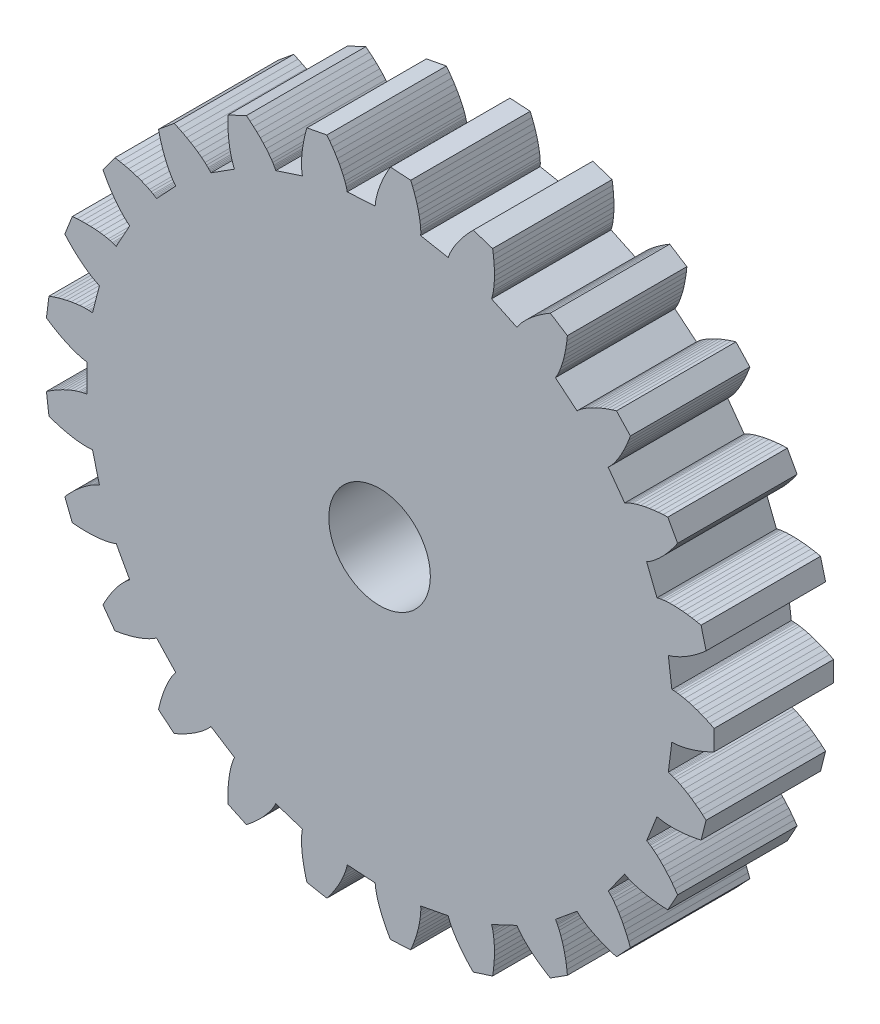
SolidWorks part; units mm, degrees
ref_plane "Front Plane" through (0, 0, 0) normal (0, 0, 1) x (1, 0, 0)
ref_plane "Top Plane" through (0, 0, 0) normal (0, 1, 0) x (1, 0, 0)
ref_plane "Right Plane" through (0, 0, 0) normal (1, 0, 0) x (0, 0, -1)
sketch "Model" plane through (0, 0, 0) normal (0, 0, 1) x (1, 0, 0)
  line L0 (22.5153, 13.4937) -> (22.5501, 13.4944)
  line L1 (22.5501, 13.4944) -> (22.5851, 13.4936)
  line L2 (22.5851, 13.4936) -> (22.6201, 13.4916)
  line L3 (22.6201, 13.4916) -> (22.6552, 13.4888)
  line L4 (22.6552, 13.4888) -> (22.7255, 13.481)
  line L5 (22.7255, 13.481) -> (22.796, 13.4706)
  line L6 (22.796, 13.4706) -> (22.9373, 13.4433)
  line L7 (22.9373, 13.4433) -> (23.079, 13.4085)
  line L8 (23.079, 13.4085) -> (23.221, 13.3669)
  line L9 (23.221, 13.3669) -> (23.363, 13.3191)
  line L10 (23.363, 13.3191) -> (23.5051, 13.2655)
  line L11 (23.5051, 13.2655) -> (23.647, 13.2062)
  line L12 (23.647, 13.2062) -> (23.7888, 13.1416)
  line L13 (23.7888, 13.1416) -> (23.9303, 13.0718)
  line L14 (23.9303, 13.0718) -> (23.9303, 12.3915)
  line L15 (23.9303, 12.3915) -> (23.7888, 12.3217)
  line L16 (23.7888, 12.3217) -> (23.647, 12.257)
  line L17 (23.647, 12.257) -> (23.5051, 12.1978)
  line L18 (23.5051, 12.1978) -> (23.363, 12.1441)
  line L19 (23.363, 12.1441) -> (23.221, 12.0963)
  line L20 (23.221, 12.0963) -> (23.079, 12.0548)
  line L21 (23.079, 12.0548) -> (22.9373, 12.0199)
  line L22 (22.9373, 12.0199) -> (22.796, 11.9927)
  line L23 (22.796, 11.9927) -> (22.7255, 11.9823)
  line L24 (22.7255, 11.9823) -> (22.6552, 11.9745)
  line L25 (22.6552, 11.9745) -> (22.6201, 11.9716)
  line L26 (22.6201, 11.9716) -> (22.5851, 11.9697)
  line L27 (22.5851, 11.9697) -> (22.5501, 11.9688)
  line L28 (22.5501, 11.9688) -> (22.5153, 11.9696)
  line L29 (22.5153, 11.9696) -> (22.3975, 11.0367)
  line L30 (22.3975, 11.0367) -> (22.4314, 11.0287)
  line L31 (22.4314, 11.0287) -> (22.465, 11.0192)
  line L32 (22.465, 11.0192) -> (22.4984, 11.0086)
  line L33 (22.4984, 11.0086) -> (22.5317, 10.9971)
  line L34 (22.5317, 10.9971) -> (22.5978, 10.9721)
  line L35 (22.5978, 10.9721) -> (22.6635, 10.9445)
  line L36 (22.6635, 10.9445) -> (22.7937, 10.8829)
  line L37 (22.7937, 10.8829) -> (22.9223, 10.8139)
  line L38 (22.9223, 10.8139) -> (23.0494, 10.7384)
  line L39 (23.0494, 10.7384) -> (23.1751, 10.6567)
  line L40 (23.1751, 10.6567) -> (23.2994, 10.5694)
  line L41 (23.2994, 10.5694) -> (23.4221, 10.4767)
  line L42 (23.4221, 10.4767) -> (23.5434, 10.3789)
  line L43 (23.5434, 10.3789) -> (23.6631, 10.2761)
  line L44 (23.6631, 10.2761) -> (23.4939, 9.6172)
  line L45 (23.4939, 9.6172) -> (23.3395, 9.5847)
  line L46 (23.3395, 9.5847) -> (23.1861, 9.5574)
  line L47 (23.1861, 9.5574) -> (23.0339, 9.5353)
  line L48 (23.0339, 9.5353) -> (22.8829, 9.5187)
  line L49 (22.8829, 9.5187) -> (22.7334, 9.5077)
  line L50 (22.7334, 9.5077) -> (22.5856, 9.5027)
  line L51 (22.5856, 9.5027) -> (22.4397, 9.5042)
  line L52 (22.4397, 9.5042) -> (22.296, 9.513)
  line L53 (22.296, 9.513) -> (22.2251, 9.5205)
  line L54 (22.2251, 9.5205) -> (22.1551, 9.5304)
  line L55 (22.1551, 9.5304) -> (22.1204, 9.5364)
  line L56 (22.1204, 9.5364) -> (22.086, 9.5432)
  line L57 (22.086, 9.5432) -> (22.0519, 9.551)
  line L58 (22.0519, 9.551) -> (22.0184, 9.5604)
  line L59 (22.0184, 9.5604) -> (21.6723, 8.6861)
  line L60 (21.6723, 8.6861) -> (21.7031, 8.67)
  line L61 (21.7031, 8.67) -> (21.7333, 8.6524)
  line L62 (21.7333, 8.6524) -> (21.7631, 8.6338)
  line L63 (21.7631, 8.6338) -> (21.7925, 8.6145)
  line L64 (21.7925, 8.6145) -> (21.8503, 8.5737)
  line L65 (21.8503, 8.5737) -> (21.9071, 8.5306)
  line L66 (21.9071, 8.5306) -> (22.0178, 8.4387)
  line L67 (22.0178, 8.4387) -> (22.1252, 8.3399)
  line L68 (22.1252, 8.3399) -> (22.2296, 8.2351)
  line L69 (22.2296, 8.2351) -> (22.331, 8.1247)
  line L70 (22.331, 8.1247) -> (22.4297, 8.0093)
  line L71 (22.4297, 8.0093) -> (22.5255, 7.889)
  line L72 (22.5255, 7.889) -> (22.6186, 7.764)
  line L73 (22.6186, 7.764) -> (22.709, 7.6347)
  line L74 (22.709, 7.6347) -> (22.3812, 7.0385)
  line L75 (22.3812, 7.0385) -> (22.2236, 7.0455)
  line L76 (22.2236, 7.0455) -> (22.0683, 7.0572)
  line L77 (22.0683, 7.0572) -> (21.9153, 7.0737)
  line L78 (21.9153, 7.0737) -> (21.765, 7.0951)
  line L79 (21.765, 7.0951) -> (21.6175, 7.1216)
  line L80 (21.6175, 7.1216) -> (21.473, 7.1536)
  line L81 (21.473, 7.1536) -> (21.3321, 7.1913)
  line L82 (21.3321, 7.1913) -> (21.1951, 7.2356)
  line L83 (21.1951, 7.2356) -> (21.1283, 7.2604)
  line L84 (21.1283, 7.2604) -> (21.0629, 7.2874)
  line L85 (21.0629, 7.2874) -> (21.0308, 7.3018)
  line L86 (21.0308, 7.3018) -> (20.9992, 7.317)
  line L87 (20.9992, 7.317) -> (20.9681, 7.3331)
  line L88 (20.9681, 7.3331) -> (20.938, 7.3505)
  line L89 (20.938, 7.3505) -> (20.3853, 6.5898)
  line L90 (20.3853, 6.5898) -> (20.4112, 6.5665)
  line L91 (20.4112, 6.5665) -> (20.4361, 6.5419)
  line L92 (20.4361, 6.5419) -> (20.4602, 6.5165)
  line L93 (20.4602, 6.5165) -> (20.4839, 6.4905)
  line L94 (20.4839, 6.4905) -> (20.5298, 6.4366)
  line L95 (20.5298, 6.4366) -> (20.574, 6.3808)
  line L96 (20.574, 6.3808) -> (20.6584, 6.2642)
  line L97 (20.6584, 6.2642) -> (20.7379, 6.1418)
  line L98 (20.7379, 6.1418) -> (20.8129, 6.0143)
  line L99 (20.8129, 6.0143) -> (20.8838, 5.8822)
  line L100 (20.8838, 5.8822) -> (20.9506, 5.7458)
  line L101 (20.9506, 5.7458) -> (21.0135, 5.6055)
  line L102 (21.0135, 5.6055) -> (21.0726, 5.4613)
  line L103 (21.0726, 5.4613) -> (21.128, 5.3136)
  line L104 (21.128, 5.3136) -> (20.6622, 4.8176)
  line L105 (20.6622, 4.8176) -> (20.5113, 4.8636)
  line L106 (20.5113, 4.8636) -> (20.3638, 4.9136)
  line L107 (20.3638, 4.9136) -> (20.2197, 4.9675)
  line L108 (20.2197, 4.9675) -> (20.0794, 5.0257)
  line L109 (20.0794, 5.0257) -> (19.9432, 5.0881)
  line L110 (19.9432, 5.0881) -> (19.8112, 5.1549)
  line L111 (19.8112, 5.1549) -> (19.6841, 5.2265)
  line L112 (19.6841, 5.2265) -> (19.5624, 5.3035)
  line L113 (19.5624, 5.3035) -> (19.5039, 5.3441)
  line L114 (19.5039, 5.3441) -> (19.4472, 5.3866)
  line L115 (19.4472, 5.3866) -> (19.4197, 5.4085)
  line L116 (19.4197, 5.4085) -> (19.3929, 5.4311)
  line L117 (19.3929, 5.4311) -> (19.3668, 5.4543)
  line L118 (19.3668, 5.4543) -> (19.3419, 5.4787)
  line L119 (19.3419, 5.4787) -> (18.6174, 4.8793)
  line L120 (18.6174, 4.8793) -> (18.6367, 4.8503)
  line L121 (18.6367, 4.8503) -> (18.6547, 4.8204)
  line L122 (18.6547, 4.8204) -> (18.6718, 4.7898)
  line L123 (18.6718, 4.7898) -> (18.6882, 4.7586)
  line L124 (18.6882, 4.7586) -> (18.7193, 4.6951)
  line L125 (18.7193, 4.6951) -> (18.7483, 4.63)
  line L126 (18.7483, 4.63) -> (18.801, 4.496)
  line L127 (18.801, 4.496) -> (18.8476, 4.3577)
  line L128 (18.8476, 4.3577) -> (18.8885, 4.2156)
  line L129 (18.8885, 4.2156) -> (18.9243, 4.07)
  line L130 (18.9243, 4.07) -> (18.9551, 3.9213)
  line L131 (18.9551, 3.9213) -> (18.9811, 3.7697)
  line L132 (18.9811, 3.7697) -> (19.0025, 3.6154)
  line L133 (19.0025, 3.6154) -> (19.0194, 3.4586)
  line L134 (19.0194, 3.4586) -> (18.445, 3.094)
  line L135 (18.445, 3.094) -> (18.3102, 3.1761)
  line L136 (18.3102, 3.1761) -> (18.1797, 3.2611)
  line L137 (18.1797, 3.2611) -> (18.0536, 3.3493)
  line L138 (18.0536, 3.3493) -> (17.9322, 3.4404)
  line L139 (17.9322, 3.4404) -> (17.8157, 3.5348)
  line L140 (17.8157, 3.5348) -> (17.7045, 3.6323)
  line L141 (17.7045, 3.6323) -> (17.5992, 3.7333)
  line L142 (17.5992, 3.7333) -> (17.5004, 3.8381)
  line L143 (17.5004, 3.8381) -> (17.4539, 3.892)
  line L144 (17.4539, 3.892) -> (17.4096, 3.9472)
  line L145 (17.4096, 3.9472) -> (17.3884, 3.9753)
  line L146 (17.3884, 3.9753) -> (17.368, 4.0038)
  line L147 (17.368, 4.0038) -> (17.3486, 4.0329)
  line L148 (17.3486, 4.0329) -> (17.3305, 4.0626)
  line L149 (17.3305, 4.0626) -> (16.4797, 3.6623)
  line L150 (16.4797, 3.6623) -> (16.4912, 3.6294)
  line L151 (16.4912, 3.6294) -> (16.5012, 3.5959)
  line L152 (16.5012, 3.5959) -> (16.5101, 3.562)
  line L153 (16.5101, 3.562) -> (16.5183, 3.5278)
  line L154 (16.5183, 3.5278) -> (16.5326, 3.4585)
  line L155 (16.5326, 3.4585) -> (16.5445, 3.3882)
  line L156 (16.5445, 3.3882) -> (16.5622, 3.2454)
  line L157 (16.5622, 3.2454) -> (16.5729, 3.0998)
  line L158 (16.5729, 3.0998) -> (16.5772, 2.952)
  line L159 (16.5772, 2.952) -> (16.5756, 2.8021)
  line L160 (16.5756, 2.8021) -> (16.5685, 2.6504)
  line L161 (16.5685, 2.6504) -> (16.556, 2.4971)
  line L162 (16.556, 2.4971) -> (16.5384, 2.3423)
  line L163 (16.5384, 2.3423) -> (16.5157, 2.1862)
  line L164 (16.5157, 2.1862) -> (15.8687, 1.9759)
  line L165 (15.8687, 1.9759) -> (15.7586, 2.0889)
  line L166 (15.7586, 2.0889) -> (15.6533, 2.2038)
  line L167 (15.6533, 2.2038) -> (15.5531, 2.3205)
  line L168 (15.5531, 2.3205) -> (15.4582, 2.439)
  line L169 (15.4582, 2.439) -> (15.3688, 2.5593)
  line L170 (15.3688, 2.5593) -> (15.2854, 2.6815)
  line L171 (15.2854, 2.6815) -> (15.2085, 2.8055)
  line L172 (15.2085, 2.8055) -> (15.1389, 2.9315)
  line L173 (15.1389, 2.9315) -> (15.1072, 2.9954)
  line L174 (15.1072, 2.9954) -> (15.078, 3.0598)
  line L175 (15.078, 3.0598) -> (15.0645, 3.0923)
  line L176 (15.0645, 3.0923) -> (15.0519, 3.125)
  line L177 (15.0519, 3.125) -> (15.0402, 3.158)
  line L178 (15.0402, 3.158) -> (15.0302, 3.1913)
  line L179 (15.0302, 3.1913) -> (14.1065, 3.0151)
  line L180 (14.1065, 3.0151) -> (14.1095, 2.9804)
  line L181 (14.1095, 2.9804) -> (14.1108, 2.9455)
  line L182 (14.1108, 2.9455) -> (14.111, 2.9104)
  line L183 (14.111, 2.9104) -> (14.1104, 2.8752)
  line L184 (14.1104, 2.8752) -> (14.107, 2.8046)
  line L185 (14.107, 2.8046) -> (14.1011, 2.7336)
  line L186 (14.1011, 2.7336) -> (14.0827, 2.5908)
  line L187 (14.0827, 2.5908) -> (14.0569, 2.4471)
  line L188 (14.0569, 2.4471) -> (14.0243, 2.3029)
  line L189 (14.0243, 2.3029) -> (13.9855, 2.1581)
  line L190 (13.9855, 2.1581) -> (13.9409, 2.0129)
  line L191 (13.9409, 2.0129) -> (13.8907, 1.8675)
  line L192 (13.8907, 1.8675) -> (13.8351, 1.722)
  line L193 (13.8351, 1.722) -> (13.7743, 1.5764)
  line L194 (13.7743, 1.5764) -> (13.0953, 1.5337)
  line L195 (13.0953, 1.5337) -> (13.0168, 1.6705)
  line L196 (13.0168, 1.6705) -> (12.9434, 1.808)
  line L197 (12.9434, 1.808) -> (12.8753, 1.9459)
  line L198 (12.8753, 1.9459) -> (12.8128, 2.0843)
  line L199 (12.8128, 2.0843) -> (12.7562, 2.2231)
  line L200 (12.7562, 2.2231) -> (12.7058, 2.3621)
  line L201 (12.7058, 2.3621) -> (12.6622, 2.5014)
  line L202 (12.6622, 2.5014) -> (12.6261, 2.6408)
  line L203 (12.6261, 2.6408) -> (12.6113, 2.7105)
  line L204 (12.6113, 2.7105) -> (12.599, 2.7801)
  line L205 (12.599, 2.7801) -> (12.594, 2.815)
  line L206 (12.594, 2.815) -> (12.5899, 2.8498)
  line L207 (12.5899, 2.8498) -> (12.5868, 2.8846)
  line L208 (12.5868, 2.8846) -> (12.5854, 2.9194)
  line L209 (12.5854, 2.9194) -> (11.6469, 2.9784)
  line L210 (11.6469, 2.9784) -> (11.6411, 2.9441)
  line L211 (11.6411, 2.9441) -> (11.6337, 2.91)
  line L212 (11.6337, 2.91) -> (11.6253, 2.8759)
  line L213 (11.6253, 2.8759) -> (11.6159, 2.842)
  line L214 (11.6159, 2.842) -> (11.595, 2.7744)
  line L215 (11.595, 2.7744) -> (11.5716, 2.7071)
  line L216 (11.5716, 2.7071) -> (11.5184, 2.5733)
  line L217 (11.5184, 2.5733) -> (11.4576, 2.4407)
  line L218 (11.4576, 2.4407) -> (11.3902, 2.309)
  line L219 (11.3902, 2.309) -> (11.3166, 2.1784)
  line L220 (11.3166, 2.1784) -> (11.2372, 2.049)
  line L221 (11.2372, 2.049) -> (11.1525, 1.9206)
  line L222 (11.1525, 1.9206) -> (11.0624, 1.7935)
  line L223 (11.0624, 1.7935) -> (10.9673, 1.6676)
  line L224 (10.9673, 1.6676) -> (10.2991, 1.7951)
  line L225 (10.2991, 1.7951) -> (10.257, 1.9471)
  line L226 (10.257, 1.9471) -> (10.2201, 2.0985)
  line L227 (10.2201, 2.0985) -> (10.1885, 2.249)
  line L228 (10.1885, 2.249) -> (10.1624, 2.3986)
  line L229 (10.1624, 2.3986) -> (10.1421, 2.5471)
  line L230 (10.1421, 2.5471) -> (10.1278, 2.6943)
  line L231 (10.1278, 2.6943) -> (10.1202, 2.8401)
  line L232 (10.1202, 2.8401) -> (10.1199, 2.984)
  line L233 (10.1199, 2.984) -> (10.1229, 3.0552)
  line L234 (10.1229, 3.0552) -> (10.1284, 3.1258)
  line L235 (10.1284, 3.1258) -> (10.1322, 3.1607)
  line L236 (10.1322, 3.1607) -> (10.1368, 3.1955)
  line L237 (10.1368, 3.1955) -> (10.1425, 3.23)
  line L238 (10.1425, 3.23) -> (10.1498, 3.264)
  line L239 (10.1498, 3.264) -> (9.2555, 3.5546)
  line L240 (9.2555, 3.5546) -> (9.2413, 3.5228)
  line L241 (9.2413, 3.5228) -> (9.2257, 3.4916)
  line L242 (9.2257, 3.4916) -> (9.209, 3.4607)
  line L243 (9.209, 3.4607) -> (9.1915, 3.4302)
  line L244 (9.1915, 3.4302) -> (9.1545, 3.3699)
  line L245 (9.1545, 3.3699) -> (9.1151, 3.3105)
  line L246 (9.1151, 3.3105) -> (9.0302, 3.1942)
  line L247 (9.0302, 3.1942) -> (8.9384, 3.0808)
  line L248 (8.9384, 3.0808) -> (8.8403, 2.9701)
  line L249 (8.8403, 2.9701) -> (8.7366, 2.8619)
  line L250 (8.7366, 2.8619) -> (8.6275, 2.7562)
  line L251 (8.6275, 2.7562) -> (8.5135, 2.653)
  line L252 (8.5135, 2.653) -> (8.3947, 2.5522)
  line L253 (8.3947, 2.5522) -> (8.2713, 2.4539)
  line L254 (8.2713, 2.4539) -> (7.6557, 2.7436)
  line L255 (7.6557, 2.7436) -> (7.6528, 2.9013)
  line L256 (7.6528, 2.9013) -> (7.6547, 3.0571)
  line L257 (7.6547, 3.0571) -> (7.6615, 3.2108)
  line L258 (7.6615, 3.2108) -> (7.6734, 3.3622)
  line L259 (7.6734, 3.3622) -> (7.6906, 3.5111)
  line L260 (7.6906, 3.5111) -> (7.7135, 3.6572)
  line L261 (7.7135, 3.6572) -> (7.7423, 3.8003)
  line L262 (7.7423, 3.8003) -> (7.7778, 3.9398)
  line L263 (7.7778, 3.9398) -> (7.7984, 4.008)
  line L264 (7.7984, 4.008) -> (7.8213, 4.0749)
  line L265 (7.8213, 4.0749) -> (7.8337, 4.1079)
  line L266 (7.8337, 4.1079) -> (7.8468, 4.1404)
  line L267 (7.8468, 4.1404) -> (7.8609, 4.1724)
  line L268 (7.8609, 4.1724) -> (7.8764, 4.2036)
  line L269 (7.8764, 4.2036) -> (7.0825, 4.7074)
  line L270 (7.0825, 4.7074) -> (7.0608, 4.6801)
  line L271 (7.0608, 4.6801) -> (7.0379, 4.6537)
  line L272 (7.0379, 4.6537) -> (7.0141, 4.628)
  line L273 (7.0141, 4.628) -> (6.9896, 4.6028)
  line L274 (6.9896, 4.6028) -> (6.9387, 4.5536)
  line L275 (6.9387, 4.5536) -> (6.8858, 4.5059)
  line L276 (6.8858, 4.5059) -> (6.7746, 4.4144)
  line L277 (6.7746, 4.4144) -> (6.6575, 4.3274)
  line L278 (6.6575, 4.3274) -> (6.535, 4.2445)
  line L279 (6.535, 4.2445) -> (6.4076, 4.1655)
  line L280 (6.4076, 4.1655) -> (6.2757, 4.0903)
  line L281 (6.2757, 4.0903) -> (6.1395, 4.0186)
  line L282 (6.1395, 4.0186) -> (5.9994, 3.9506)
  line L283 (5.9994, 3.9506) -> (5.8554, 3.8861)
  line L284 (5.8554, 3.8861) -> (5.3312, 4.3197)
  line L285 (5.3312, 4.3197) -> (5.3676, 4.4732)
  line L286 (5.3676, 4.4732) -> (5.4082, 4.6237)
  line L287 (5.4082, 4.6237) -> (5.453, 4.7708)
  line L288 (5.453, 4.7708) -> (5.5022, 4.9145)
  line L289 (5.5022, 4.9145) -> (5.556, 5.0544)
  line L290 (5.556, 5.0544) -> (5.6144, 5.1903)
  line L291 (5.6144, 5.1903) -> (5.6779, 5.3217)
  line L292 (5.6779, 5.3217) -> (5.747, 5.4479)
  line L293 (5.747, 5.4479) -> (5.7839, 5.5089)
  line L294 (5.7839, 5.5089) -> (5.8227, 5.5681)
  line L295 (5.8227, 5.5681) -> (5.8429, 5.5969)
  line L296 (5.8429, 5.5969) -> (5.8637, 5.6251)
  line L297 (5.8637, 5.6251) -> (5.8853, 5.6526)
  line L298 (5.8853, 5.6526) -> (5.9081, 5.6789)
  line L299 (5.9081, 5.6789) -> (5.2644, 6.3644)
  line L300 (5.2644, 6.3644) -> (5.2367, 6.3433)
  line L301 (5.2367, 6.3433) -> (5.2079, 6.3235)
  line L302 (5.2079, 6.3235) -> (5.1784, 6.3045)
  line L303 (5.1784, 6.3045) -> (5.1484, 6.2862)
  line L304 (5.1484, 6.2862) -> (5.0869, 6.2512)
  line L305 (5.0869, 6.2512) -> (5.0238, 6.2181)
  line L306 (5.0238, 6.2181) -> (4.8934, 6.1571)
  line L307 (4.8934, 6.1571) -> (4.7583, 6.102)
  line L308 (4.7583, 6.102) -> (4.619, 6.0522)
  line L309 (4.619, 6.0522) -> (4.476, 6.0074)
  line L310 (4.476, 6.0074) -> (4.3295, 5.9673)
  line L311 (4.3295, 5.9673) -> (4.1798, 5.9318)
  line L312 (4.1798, 5.9318) -> (4.0272, 5.9007)
  line L313 (4.0272, 5.9007) -> (3.8717, 5.874)
  line L314 (3.8717, 5.874) -> (3.4718, 6.4244)
  line L315 (3.4718, 6.4244) -> (3.5452, 6.5641)
  line L316 (3.5452, 6.5641) -> (3.6219, 6.6996)
  line L317 (3.6219, 6.6996) -> (3.7019, 6.831)
  line L318 (3.7019, 6.831) -> (3.7853, 6.9579)
  line L319 (3.7853, 6.9579) -> (3.8721, 7.0801)
  line L320 (3.8721, 7.0801) -> (3.9625, 7.1972)
  line L321 (3.9625, 7.1972) -> (4.0567, 7.3086)
  line L322 (4.0567, 7.3086) -> (4.1551, 7.4138)
  line L323 (4.1551, 7.4138) -> (4.206, 7.4636)
  line L324 (4.206, 7.4636) -> (4.2583, 7.5113)
  line L325 (4.2583, 7.5113) -> (4.285, 7.5342)
  line L326 (4.285, 7.5342) -> (4.3122, 7.5563)
  line L327 (4.3122, 7.5563) -> (4.3399, 7.5776)
  line L328 (4.3399, 7.5776) -> (4.3685, 7.5975)
  line L329 (4.3685, 7.5975) -> (3.9155, 8.4215)
  line L330 (3.9155, 8.4215) -> (3.8834, 8.4079)
  line L331 (3.8834, 8.4079) -> (3.8506, 8.3959)
  line L332 (3.8506, 8.3959) -> (3.8174, 8.3848)
  line L333 (3.8174, 8.3848) -> (3.7837, 8.3745)
  line L334 (3.7837, 8.3745) -> (3.7154, 8.3559)
  line L335 (3.7154, 8.3559) -> (3.6461, 8.3396)
  line L336 (3.6461, 8.3396) -> (3.5046, 8.3129)
  line L337 (3.5046, 8.3129) -> (3.36, 8.2932)
  line L338 (3.36, 8.2932) -> (3.2127, 8.2796)
  line L339 (3.2127, 8.2796) -> (3.0631, 8.2717)
  line L340 (3.0631, 8.2717) -> (2.9112, 8.2693)
  line L341 (2.9112, 8.2693) -> (2.7574, 8.2721)
  line L342 (2.7574, 8.2721) -> (2.6018, 8.28)
  line L343 (2.6018, 8.28) -> (2.4446, 8.2928)
  line L344 (2.4446, 8.2928) -> (2.1941, 8.9254)
  line L345 (2.1941, 8.9254) -> (2.3, 9.0424)
  line L346 (2.3, 9.0424) -> (2.408, 9.1547)
  line L347 (2.408, 9.1547) -> (2.5182, 9.262)
  line L348 (2.5182, 9.262) -> (2.6305, 9.3642)
  line L349 (2.6305, 9.3642) -> (2.745, 9.4609)
  line L350 (2.745, 9.4609) -> (2.8617, 9.5518)
  line L351 (2.8617, 9.5518) -> (2.9806, 9.6364)
  line L352 (2.9806, 9.6364) -> (3.102, 9.7138)
  line L353 (3.102, 9.7138) -> (3.1637, 9.7494)
  line L354 (3.1637, 9.7494) -> (3.2262, 9.7825)
  line L355 (3.2262, 9.7825) -> (3.2578, 9.7981)
  line L356 (3.2578, 9.7981) -> (3.2897, 9.8128)
  line L357 (3.2897, 9.8128) -> (3.3218, 9.8265)
  line L358 (3.3218, 9.8265) -> (3.3544, 9.8386)
  line L359 (3.3544, 9.8386) -> (3.1206, 10.7493)
  line L360 (3.1206, 10.7493) -> (3.0862, 10.7442)
  line L361 (3.0862, 10.7442) -> (3.0514, 10.7407)
  line L362 (3.0514, 10.7407) -> (3.0164, 10.7383)
  line L363 (3.0164, 10.7383) -> (2.9813, 10.7367)
  line L364 (2.9813, 10.7367) -> (2.9105, 10.7356)
  line L365 (2.9105, 10.7356) -> (2.8393, 10.7371)
  line L366 (2.8393, 10.7371) -> (2.6956, 10.7464)
  line L367 (2.6956, 10.7464) -> (2.5506, 10.7632)
  line L368 (2.5506, 10.7632) -> (2.4046, 10.7867)
  line L369 (2.4046, 10.7867) -> (2.2577, 10.8163)
  line L370 (2.2577, 10.8163) -> (2.11, 10.8517)
  line L371 (2.11, 10.8517) -> (1.9618, 10.8927)
  line L372 (1.9618, 10.8927) -> (1.813, 10.9391)
  line L373 (1.813, 10.9391) -> (1.6639, 10.9906)
  line L374 (1.6639, 10.9906) -> (1.5786, 11.6655)
  line L375 (1.5786, 11.6655) -> (1.7103, 11.7525)
  line L376 (1.7103, 11.7525) -> (1.8428, 11.8344)
  line L377 (1.8428, 11.8344) -> (1.9762, 11.911)
  line L378 (1.9762, 11.911) -> (2.1104, 11.982)
  line L379 (2.1104, 11.982) -> (2.2454, 12.0472)
  line L380 (2.2454, 12.0472) -> (2.381, 12.1063)
  line L381 (2.381, 12.1063) -> (2.5172, 12.1586)
  line L382 (2.5172, 12.1586) -> (2.654, 12.2034)
  line L383 (2.654, 12.2034) -> (2.7227, 12.2225)
  line L384 (2.7227, 12.2225) -> (2.7915, 12.2391)
  line L385 (2.7915, 12.2391) -> (2.8259, 12.2463)
  line L386 (2.8259, 12.2463) -> (2.8604, 12.2526)
  line L387 (2.8604, 12.2526) -> (2.8949, 12.2578)
  line L388 (2.8949, 12.2578) -> (2.9296, 12.2615)
  line L389 (2.9296, 12.2615) -> (2.9296, 13.2018)
  line L390 (2.9296, 13.2018) -> (2.8949, 13.2054)
  line L391 (2.8949, 13.2054) -> (2.8604, 13.2107)
  line L392 (2.8604, 13.2107) -> (2.8259, 13.217)
  line L393 (2.8259, 13.217) -> (2.7915, 13.2242)
  line L394 (2.7915, 13.2242) -> (2.7227, 13.2408)
  line L395 (2.7227, 13.2408) -> (2.654, 13.2599)
  line L396 (2.654, 13.2599) -> (2.5172, 13.3047)
  line L397 (2.5172, 13.3047) -> (2.381, 13.357)
  line L398 (2.381, 13.357) -> (2.2454, 13.416)
  line L399 (2.2454, 13.416) -> (2.1104, 13.4812)
  line L400 (2.1104, 13.4812) -> (1.9762, 13.5523)
  line L401 (1.9762, 13.5523) -> (1.8428, 13.6289)
  line L402 (1.8428, 13.6289) -> (1.7103, 13.7107)
  line L403 (1.7103, 13.7107) -> (1.5786, 13.7977)
  line L404 (1.5786, 13.7977) -> (1.6639, 14.4727)
  line L405 (1.6639, 14.4727) -> (1.813, 14.5242)
  line L406 (1.813, 14.5242) -> (1.9618, 14.5705)
  line L407 (1.9618, 14.5705) -> (2.11, 14.6115)
  line L408 (2.11, 14.6115) -> (2.2577, 14.647)
  line L409 (2.2577, 14.647) -> (2.4046, 14.6766)
  line L410 (2.4046, 14.6766) -> (2.5506, 14.7)
  line L411 (2.5506, 14.7) -> (2.6956, 14.7168)
  line L412 (2.6956, 14.7168) -> (2.8393, 14.7261)
  line L413 (2.8393, 14.7261) -> (2.9105, 14.7276)
  line L414 (2.9105, 14.7276) -> (2.9813, 14.7266)
  line L415 (2.9813, 14.7266) -> (3.0164, 14.725)
  line L416 (3.0164, 14.725) -> (3.0514, 14.7225)
  line L417 (3.0514, 14.7225) -> (3.0862, 14.719)
  line L418 (3.0862, 14.719) -> (3.1206, 14.7139)
  line L419 (3.1206, 14.7139) -> (3.3544, 15.6247)
  line L420 (3.3544, 15.6247) -> (3.3218, 15.6368)
  line L421 (3.3218, 15.6368) -> (3.2897, 15.6505)
  line L422 (3.2897, 15.6505) -> (3.2578, 15.6652)
  line L423 (3.2578, 15.6652) -> (3.2262, 15.6807)
  line L424 (3.2262, 15.6807) -> (3.1637, 15.7139)
  line L425 (3.1637, 15.7139) -> (3.102, 15.7495)
  line L426 (3.102, 15.7495) -> (2.9806, 15.8269)
  line L427 (2.9806, 15.8269) -> (2.8617, 15.9114)
  line L428 (2.8617, 15.9114) -> (2.745, 16.0023)
  line L429 (2.745, 16.0023) -> (2.6305, 16.0991)
  line L430 (2.6305, 16.0991) -> (2.5182, 16.2013)
  line L431 (2.5182, 16.2013) -> (2.408, 16.3086)
  line L432 (2.408, 16.3086) -> (2.3, 16.4209)
  line L433 (2.3, 16.4209) -> (2.1941, 16.5379)
  line L434 (2.1941, 16.5379) -> (2.4446, 17.1704)
  line L435 (2.4446, 17.1704) -> (2.6018, 17.1832)
  line L436 (2.6018, 17.1832) -> (2.7574, 17.1911)
  line L437 (2.7574, 17.1911) -> (2.9112, 17.1939)
  line L438 (2.9112, 17.1939) -> (3.0631, 17.1915)
  line L439 (3.0631, 17.1915) -> (3.2127, 17.1837)
  line L440 (3.2127, 17.1837) -> (3.36, 17.1701)
  line L441 (3.36, 17.1701) -> (3.5046, 17.1503)
  line L442 (3.5046, 17.1503) -> (3.6461, 17.1236)
  line L443 (3.6461, 17.1236) -> (3.7154, 17.1073)
  line L444 (3.7154, 17.1073) -> (3.7837, 17.0887)
  line L445 (3.7837, 17.0887) -> (3.8174, 17.0784)
  line L446 (3.8174, 17.0784) -> (3.8506, 17.0674)
  line L447 (3.8506, 17.0674) -> (3.8834, 17.0553)
  line L448 (3.8834, 17.0553) -> (3.9155, 17.0418)
  line L449 (3.9155, 17.0418) -> (4.3685, 17.8658)
  line L450 (4.3685, 17.8658) -> (4.3399, 17.8857)
  line L451 (4.3399, 17.8857) -> (4.3122, 17.9069)
  line L452 (4.3122, 17.9069) -> (4.285, 17.9291)
  line L453 (4.285, 17.9291) -> (4.2583, 17.952)
  line L454 (4.2583, 17.952) -> (4.206, 17.9996)
  line L455 (4.206, 17.9996) -> (4.1551, 18.0495)
  line L456 (4.1551, 18.0495) -> (4.0567, 18.1546)
  line L457 (4.0567, 18.1546) -> (3.9625, 18.2661)
  line L458 (3.9625, 18.2661) -> (3.8721, 18.3831)
  line L459 (3.8721, 18.3831) -> (3.7853, 18.5053)
  line L460 (3.7853, 18.5053) -> (3.7019, 18.6322)
  line L461 (3.7019, 18.6322) -> (3.6219, 18.7636)
  line L462 (3.6219, 18.7636) -> (3.5452, 18.8992)
  line L463 (3.5452, 18.8992) -> (3.4718, 19.0388)
  line L464 (3.4718, 19.0388) -> (3.8717, 19.5892)
  line L465 (3.8717, 19.5892) -> (4.0272, 19.5626)
  line L466 (4.0272, 19.5626) -> (4.1798, 19.5315)
  line L467 (4.1798, 19.5315) -> (4.3295, 19.496)
  line L468 (4.3295, 19.496) -> (4.476, 19.4559)
  line L469 (4.476, 19.4559) -> (4.619, 19.4111)
  line L470 (4.619, 19.4111) -> (4.7583, 19.3613)
  line L471 (4.7583, 19.3613) -> (4.8934, 19.3062)
  line L472 (4.8934, 19.3062) -> (5.0238, 19.2451)
  line L473 (5.0238, 19.2451) -> (5.0869, 19.2121)
  line L474 (5.0869, 19.2121) -> (5.1484, 19.1771)
  line L475 (5.1484, 19.1771) -> (5.1784, 19.1588)
  line L476 (5.1784, 19.1588) -> (5.2079, 19.1398)
  line L477 (5.2079, 19.1398) -> (5.2367, 19.1199)
  line L478 (5.2367, 19.1199) -> (5.2644, 19.0989)
  line L479 (5.2644, 19.0989) -> (5.9081, 19.7843)
  line L480 (5.9081, 19.7843) -> (5.8853, 19.8107)
  line L481 (5.8853, 19.8107) -> (5.8637, 19.8381)
  line L482 (5.8637, 19.8381) -> (5.8429, 19.8664)
  line L483 (5.8429, 19.8664) -> (5.8227, 19.8952)
  line L484 (5.8227, 19.8952) -> (5.7839, 19.9544)
  line L485 (5.7839, 19.9544) -> (5.747, 20.0153)
  line L486 (5.747, 20.0153) -> (5.6779, 20.1416)
  line L487 (5.6779, 20.1416) -> (5.6144, 20.273)
  line L488 (5.6144, 20.273) -> (5.556, 20.4089)
  line L489 (5.556, 20.4089) -> (5.5022, 20.5488)
  line L490 (5.5022, 20.5488) -> (5.453, 20.6925)
  line L491 (5.453, 20.6925) -> (5.4082, 20.8396)
  line L492 (5.4082, 20.8396) -> (5.3676, 20.99)
  line L493 (5.3676, 20.99) -> (5.3312, 21.1435)
  line L494 (5.3312, 21.1435) -> (5.8554, 21.5772)
  line L495 (5.8554, 21.5772) -> (5.9994, 21.5127)
  line L496 (5.9994, 21.5127) -> (6.1395, 21.4446)
  line L497 (6.1395, 21.4446) -> (6.2757, 21.373)
  line L498 (6.2757, 21.373) -> (6.4076, 21.2977)
  line L499 (6.4076, 21.2977) -> (6.535, 21.2188)
  line L500 (6.535, 21.2188) -> (6.6575, 21.1359)
  line L501 (6.6575, 21.1359) -> (6.7746, 21.0489)
  line L502 (6.7746, 21.0489) -> (6.8858, 20.9574)
  line L503 (6.8858, 20.9574) -> (6.9387, 20.9097)
  line L504 (6.9387, 20.9097) -> (6.9896, 20.8605)
  line L505 (6.9896, 20.8605) -> (7.0141, 20.8352)
  line L506 (7.0141, 20.8352) -> (7.0379, 20.8095)
  line L507 (7.0379, 20.8095) -> (7.0608, 20.7831)
  line L508 (7.0608, 20.7831) -> (7.0825, 20.7559)
  line L509 (7.0825, 20.7559) -> (7.8764, 21.2597)
  line L510 (7.8764, 21.2597) -> (7.8609, 21.2909)
  line L511 (7.8609, 21.2909) -> (7.8468, 21.3229)
  line L512 (7.8468, 21.3229) -> (7.8337, 21.3554)
  line L513 (7.8337, 21.3554) -> (7.8213, 21.3883)
  line L514 (7.8213, 21.3883) -> (7.7984, 21.4553)
  line L515 (7.7984, 21.4553) -> (7.7778, 21.5235)
  line L516 (7.7778, 21.5235) -> (7.7423, 21.663)
  line L517 (7.7423, 21.663) -> (7.7135, 21.806)
  line L518 (7.7135, 21.806) -> (7.6906, 21.9522)
  line L519 (7.6906, 21.9522) -> (7.6734, 22.1011)
  line L520 (7.6734, 22.1011) -> (7.6615, 22.2525)
  line L521 (7.6615, 22.2525) -> (7.6547, 22.4061)
  line L522 (7.6547, 22.4061) -> (7.6528, 22.5619)
  line L523 (7.6528, 22.5619) -> (7.6557, 22.7196)
  line L524 (7.6557, 22.7196) -> (8.2713, 23.0093)
  line L525 (8.2713, 23.0093) -> (8.3947, 22.911)
  line L526 (8.3947, 22.911) -> (8.5135, 22.8103)
  line L527 (8.5135, 22.8103) -> (8.6275, 22.707)
  line L528 (8.6275, 22.707) -> (8.7366, 22.6013)
  line L529 (8.7366, 22.6013) -> (8.8403, 22.4932)
  line L530 (8.8403, 22.4932) -> (8.9384, 22.3824)
  line L531 (8.9384, 22.3824) -> (9.0302, 22.269)
  line L532 (9.0302, 22.269) -> (9.1151, 22.1527)
  line L533 (9.1151, 22.1527) -> (9.1545, 22.0934)
  line L534 (9.1545, 22.0934) -> (9.1915, 22.0331)
  line L535 (9.1915, 22.0331) -> (9.209, 22.0026)
  line L536 (9.209, 22.0026) -> (9.2257, 21.9717)
  line L537 (9.2257, 21.9717) -> (9.2413, 21.9405)
  line L538 (9.2413, 21.9405) -> (9.2555, 21.9086)
  line L539 (9.2555, 21.9086) -> (10.1498, 22.1992)
  line L540 (10.1498, 22.1992) -> (10.1425, 22.2333)
  line L541 (10.1425, 22.2333) -> (10.1368, 22.2677)
  line L542 (10.1368, 22.2677) -> (10.1322, 22.3025)
  line L543 (10.1322, 22.3025) -> (10.1284, 22.3375)
  line L544 (10.1284, 22.3375) -> (10.1229, 22.408)
  line L545 (10.1229, 22.408) -> (10.1199, 22.4792)
  line L546 (10.1199, 22.4792) -> (10.1202, 22.6232)
  line L547 (10.1202, 22.6232) -> (10.1278, 22.7689)
  line L548 (10.1278, 22.7689) -> (10.1421, 22.9161)
  line L549 (10.1421, 22.9161) -> (10.1624, 23.0646)
  line L550 (10.1624, 23.0646) -> (10.1885, 23.2142)
  line L551 (10.1885, 23.2142) -> (10.2201, 23.3648)
  line L552 (10.2201, 23.3648) -> (10.257, 23.5161)
  line L553 (10.257, 23.5161) -> (10.2991, 23.6682)
  line L554 (10.2991, 23.6682) -> (10.9673, 23.7957)
  line L555 (10.9673, 23.7957) -> (11.0624, 23.6698)
  line L556 (11.0624, 23.6698) -> (11.1525, 23.5426)
  line L557 (11.1525, 23.5426) -> (11.2372, 23.4143)
  line L558 (11.2372, 23.4143) -> (11.3166, 23.2848)
  line L559 (11.3166, 23.2848) -> (11.3902, 23.1542)
  line L560 (11.3902, 23.1542) -> (11.4576, 23.0226)
  line L561 (11.4576, 23.0226) -> (11.5184, 22.8899)
  line L562 (11.5184, 22.8899) -> (11.5716, 22.7562)
  line L563 (11.5716, 22.7562) -> (11.595, 22.6889)
  line L564 (11.595, 22.6889) -> (11.6159, 22.6213)
  line L565 (11.6159, 22.6213) -> (11.6253, 22.5873)
  line L566 (11.6253, 22.5873) -> (11.6337, 22.5533)
  line L567 (11.6337, 22.5533) -> (11.6411, 22.5191)
  line L568 (11.6411, 22.5191) -> (11.6469, 22.4848)
  line L569 (11.6469, 22.4848) -> (12.5854, 22.5439)
  line L570 (12.5854, 22.5439) -> (12.5868, 22.5786)
  line L571 (12.5868, 22.5786) -> (12.5899, 22.6135)
  line L572 (12.5899, 22.6135) -> (12.594, 22.6483)
  line L573 (12.594, 22.6483) -> (12.599, 22.6831)
  line L574 (12.599, 22.6831) -> (12.6113, 22.7528)
  line L575 (12.6113, 22.7528) -> (12.6261, 22.8225)
  line L576 (12.6261, 22.8225) -> (12.6622, 22.9619)
  line L577 (12.6622, 22.9619) -> (12.7058, 23.1011)
  line L578 (12.7058, 23.1011) -> (12.7562, 23.2402)
  line L579 (12.7562, 23.2402) -> (12.8128, 23.3789)
  line L580 (12.8128, 23.3789) -> (12.8753, 23.5174)
  line L581 (12.8753, 23.5174) -> (12.9434, 23.6553)
  line L582 (12.9434, 23.6553) -> (13.0168, 23.7927)
  line L583 (13.0168, 23.7927) -> (13.0953, 23.9296)
  line L584 (13.0953, 23.9296) -> (13.7743, 23.8868)
  line L585 (13.7743, 23.8868) -> (13.8351, 23.7412)
  line L586 (13.8351, 23.7412) -> (13.8907, 23.5957)
  line L587 (13.8907, 23.5957) -> (13.9409, 23.4503)
  line L588 (13.9409, 23.4503) -> (13.9855, 23.3052)
  line L589 (13.9855, 23.3052) -> (14.0243, 23.1604)
  line L590 (14.0243, 23.1604) -> (14.0569, 23.0161)
  line L591 (14.0569, 23.0161) -> (14.0827, 22.8725)
  line L592 (14.0827, 22.8725) -> (14.1011, 22.7297)
  line L593 (14.1011, 22.7297) -> (14.107, 22.6587)
  line L594 (14.107, 22.6587) -> (14.1104, 22.588)
  line L595 (14.1104, 22.588) -> (14.111, 22.5528)
  line L596 (14.111, 22.5528) -> (14.1108, 22.5178)
  line L597 (14.1108, 22.5178) -> (14.1095, 22.4828)
  line L598 (14.1095, 22.4828) -> (14.1065, 22.4482)
  line L599 (14.1065, 22.4482) -> (15.0302, 22.272)
  line L600 (15.0302, 22.272) -> (15.0402, 22.3053)
  line L601 (15.0402, 22.3053) -> (15.0519, 22.3382)
  line L602 (15.0519, 22.3382) -> (15.0645, 22.3709)
  line L603 (15.0645, 22.3709) -> (15.078, 22.4034)
  line L604 (15.078, 22.4034) -> (15.1072, 22.4679)
  line L605 (15.1072, 22.4679) -> (15.1389, 22.5317)
  line L606 (15.1389, 22.5317) -> (15.2085, 22.6577)
  line L607 (15.2085, 22.6577) -> (15.2854, 22.7818)
  line L608 (15.2854, 22.7818) -> (15.3688, 22.9039)
  line L609 (15.3688, 22.9039) -> (15.4582, 23.0242)
  line L610 (15.4582, 23.0242) -> (15.5531, 23.1428)
  line L611 (15.5531, 23.1428) -> (15.6533, 23.2595)
  line L612 (15.6533, 23.2595) -> (15.7586, 23.3743)
  line L613 (15.7586, 23.3743) -> (15.8687, 23.4873)
  line L614 (15.8687, 23.4873) -> (16.5157, 23.2771)
  line L615 (16.5157, 23.2771) -> (16.5384, 23.1209)
  line L616 (16.5384, 23.1209) -> (16.556, 22.9662)
  line L617 (16.556, 22.9662) -> (16.5685, 22.8128)
  line L618 (16.5685, 22.8128) -> (16.5756, 22.6612)
  line L619 (16.5756, 22.6612) -> (16.5772, 22.5113)
  line L620 (16.5772, 22.5113) -> (16.5729, 22.3634)
  line L621 (16.5729, 22.3634) -> (16.5622, 22.2179)
  line L622 (16.5622, 22.2179) -> (16.5445, 22.075)
  line L623 (16.5445, 22.075) -> (16.5326, 22.0048)
  line L624 (16.5326, 22.0048) -> (16.5183, 21.9355)
  line L625 (16.5183, 21.9355) -> (16.5101, 21.9012)
  line L626 (16.5101, 21.9012) -> (16.5012, 21.8673)
  line L627 (16.5012, 21.8673) -> (16.4912, 21.8338)
  line L628 (16.4912, 21.8338) -> (16.4797, 21.801)
  line L629 (16.4797, 21.801) -> (17.3305, 21.4006)
  line L630 (17.3305, 21.4006) -> (17.3486, 21.4304)
  line L631 (17.3486, 21.4304) -> (17.368, 21.4594)
  line L632 (17.368, 21.4594) -> (17.3884, 21.4879)
  line L633 (17.3884, 21.4879) -> (17.4096, 21.5161)
  line L634 (17.4096, 21.5161) -> (17.4539, 21.5712)
  line L635 (17.4539, 21.5712) -> (17.5004, 21.6252)
  line L636 (17.5004, 21.6252) -> (17.5992, 21.7299)
  line L637 (17.5992, 21.7299) -> (17.7045, 21.8309)
  line L638 (17.7045, 21.8309) -> (17.8157, 21.9285)
  line L639 (17.8157, 21.9285) -> (17.9322, 22.0228)
  line L640 (17.9322, 22.0228) -> (18.0536, 22.114)
  line L641 (18.0536, 22.114) -> (18.1797, 22.2021)
  line L642 (18.1797, 22.2021) -> (18.3102, 22.2872)
  line L643 (18.3102, 22.2872) -> (18.445, 22.3692)
  line L644 (18.445, 22.3692) -> (19.0194, 22.0047)
  line L645 (19.0194, 22.0047) -> (19.0025, 21.8478)
  line L646 (19.0025, 21.8478) -> (18.9811, 21.6935)
  line L647 (18.9811, 21.6935) -> (18.9551, 21.5419)
  line L648 (18.9551, 21.5419) -> (18.9243, 21.3932)
  line L649 (18.9243, 21.3932) -> (18.8885, 21.2477)
  line L650 (18.8885, 21.2477) -> (18.8476, 21.1055)
  line L651 (18.8476, 21.1055) -> (18.801, 20.9672)
  line L652 (18.801, 20.9672) -> (18.7483, 20.8333)
  line L653 (18.7483, 20.8333) -> (18.7193, 20.7682)
  line L654 (18.7193, 20.7682) -> (18.6882, 20.7046)
  line L655 (18.6882, 20.7046) -> (18.6718, 20.6735)
  line L656 (18.6718, 20.6735) -> (18.6547, 20.6429)
  line L657 (18.6547, 20.6429) -> (18.6367, 20.6129)
  line L658 (18.6367, 20.6129) -> (18.6174, 20.5839)
  line L659 (18.6174, 20.5839) -> (19.3419, 19.9846)
  line L660 (19.3419, 19.9846) -> (19.3668, 20.0089)
  line L661 (19.3668, 20.0089) -> (19.3929, 20.0322)
  line L662 (19.3929, 20.0322) -> (19.4197, 20.0547)
  line L663 (19.4197, 20.0547) -> (19.4472, 20.0767)
  line L664 (19.4472, 20.0767) -> (19.5039, 20.1191)
  line L665 (19.5039, 20.1191) -> (19.5624, 20.1598)
  line L666 (19.5624, 20.1598) -> (19.6841, 20.2367)
  line L667 (19.6841, 20.2367) -> (19.8112, 20.3083)
  line L668 (19.8112, 20.3083) -> (19.9432, 20.3752)
  line L669 (19.9432, 20.3752) -> (20.0794, 20.4376)
  line L670 (20.0794, 20.4376) -> (20.2197, 20.4957)
  line L671 (20.2197, 20.4957) -> (20.3638, 20.5497)
  line L672 (20.3638, 20.5497) -> (20.5113, 20.5996)
  line L673 (20.5113, 20.5996) -> (20.6622, 20.6456)
  line L674 (20.6622, 20.6456) -> (21.128, 20.1497)
  line L675 (21.128, 20.1497) -> (21.0726, 20.0019)
  line L676 (21.0726, 20.0019) -> (21.0135, 19.8578)
  line L677 (21.0135, 19.8578) -> (20.9506, 19.7174)
  line L678 (20.9506, 19.7174) -> (20.8838, 19.5811)
  line L679 (20.8838, 19.5811) -> (20.8129, 19.449)
  line L680 (20.8129, 19.449) -> (20.7379, 19.3215)
  line L681 (20.7379, 19.3215) -> (20.6584, 19.1991)
  line L682 (20.6584, 19.1991) -> (20.574, 19.0825)
  line L683 (20.574, 19.0825) -> (20.5298, 19.0266)
  line L684 (20.5298, 19.0266) -> (20.4839, 18.9728)
  line L685 (20.4839, 18.9728) -> (20.4602, 18.9467)
  line L686 (20.4602, 18.9467) -> (20.4361, 18.9213)
  line L687 (20.4361, 18.9213) -> (20.4112, 18.8968)
  line L688 (20.4112, 18.8968) -> (20.3853, 18.8735)
  line L689 (20.3853, 18.8735) -> (20.938, 18.1128)
  line L690 (20.938, 18.1128) -> (20.9681, 18.1302)
  line L691 (20.9681, 18.1302) -> (20.9992, 18.1462)
  line L692 (20.9992, 18.1462) -> (21.0308, 18.1614)
  line L693 (21.0308, 18.1614) -> (21.0629, 18.1758)
  line L694 (21.0629, 18.1758) -> (21.1283, 18.2028)
  line L695 (21.1283, 18.2028) -> (21.1951, 18.2277)
  line L696 (21.1951, 18.2277) -> (21.3321, 18.2719)
  line L697 (21.3321, 18.2719) -> (21.473, 18.3097)
  line L698 (21.473, 18.3097) -> (21.6175, 18.3416)
  line L699 (21.6175, 18.3416) -> (21.765, 18.3682)
  line L700 (21.765, 18.3682) -> (21.9153, 18.3896)
  line L701 (21.9153, 18.3896) -> (22.0683, 18.406)
  line L702 (22.0683, 18.406) -> (22.2236, 18.4177)
  line L703 (22.2236, 18.4177) -> (22.3812, 18.4247)
  line L704 (22.3812, 18.4247) -> (22.709, 17.8285)
  line L705 (22.709, 17.8285) -> (22.6186, 17.6992)
  line L706 (22.6186, 17.6992) -> (22.5255, 17.5743)
  line L707 (22.5255, 17.5743) -> (22.4297, 17.454)
  line L708 (22.4297, 17.454) -> (22.331, 17.3385)
  line L709 (22.331, 17.3385) -> (22.2296, 17.2282)
  line L710 (22.2296, 17.2282) -> (22.1252, 17.1234)
  line L711 (22.1252, 17.1234) -> (22.0178, 17.0246)
  line L712 (22.0178, 17.0246) -> (21.9071, 16.9326)
  line L713 (21.9071, 16.9326) -> (21.8503, 16.8896)
  line L714 (21.8503, 16.8896) -> (21.7925, 16.8488)
  line L715 (21.7925, 16.8488) -> (21.7631, 16.8294)
  line L716 (21.7631, 16.8294) -> (21.7333, 16.8109)
  line L717 (21.7333, 16.8109) -> (21.7031, 16.7933)
  line L718 (21.7031, 16.7933) -> (21.6723, 16.7771)
  line L719 (21.6723, 16.7771) -> (22.0184, 15.9029)
  line L720 (22.0184, 15.9029) -> (22.0519, 15.9122)
  line L721 (22.0519, 15.9122) -> (22.086, 15.9201)
  line L722 (22.086, 15.9201) -> (22.1204, 15.9269)
  line L723 (22.1204, 15.9269) -> (22.1551, 15.9329)
  line L724 (22.1551, 15.9329) -> (22.2251, 15.9428)
  line L725 (22.2251, 15.9428) -> (22.296, 15.9503)
  line L726 (22.296, 15.9503) -> (22.4397, 15.959)
  line L727 (22.4397, 15.959) -> (22.5856, 15.9605)
  line L728 (22.5856, 15.9605) -> (22.7334, 15.9556)
  line L729 (22.7334, 15.9556) -> (22.8829, 15.9446)
  line L730 (22.8829, 15.9446) -> (23.0339, 15.9279)
  line L731 (23.0339, 15.9279) -> (23.1861, 15.9059)
  line L732 (23.1861, 15.9059) -> (23.3395, 15.8785)
  line L733 (23.3395, 15.8785) -> (23.4939, 15.8461)
  line L734 (23.4939, 15.8461) -> (23.6631, 15.1871)
  line L735 (23.6631, 15.1871) -> (23.5434, 15.0844)
  line L736 (23.5434, 15.0844) -> (23.4221, 14.9865)
  line L737 (23.4221, 14.9865) -> (23.2994, 14.8938)
  line L738 (23.2994, 14.8938) -> (23.1751, 14.8065)
  line L739 (23.1751, 14.8065) -> (23.0494, 14.7249)
  line L740 (23.0494, 14.7249) -> (22.9223, 14.6493)
  line L741 (22.9223, 14.6493) -> (22.7937, 14.5803)
  line L742 (22.7937, 14.5803) -> (22.6635, 14.5188)
  line L743 (22.6635, 14.5188) -> (22.5978, 14.4912)
  line L744 (22.5978, 14.4912) -> (22.5317, 14.4661)
  line L745 (22.5317, 14.4661) -> (22.4984, 14.4547)
  line L746 (22.4984, 14.4547) -> (22.465, 14.4441)
  line L747 (22.465, 14.4441) -> (22.4314, 14.4345)
  line L748 (22.4314, 14.4345) -> (22.3975, 14.4266)
  line L749 (22.3975, 14.4266) -> (22.5153, 13.4937)
  circle A0 centre (12.7316, 12.7316) radius 1.7
extrude "Boss-Extrude1" add sketch "Model" along normal blind 4
